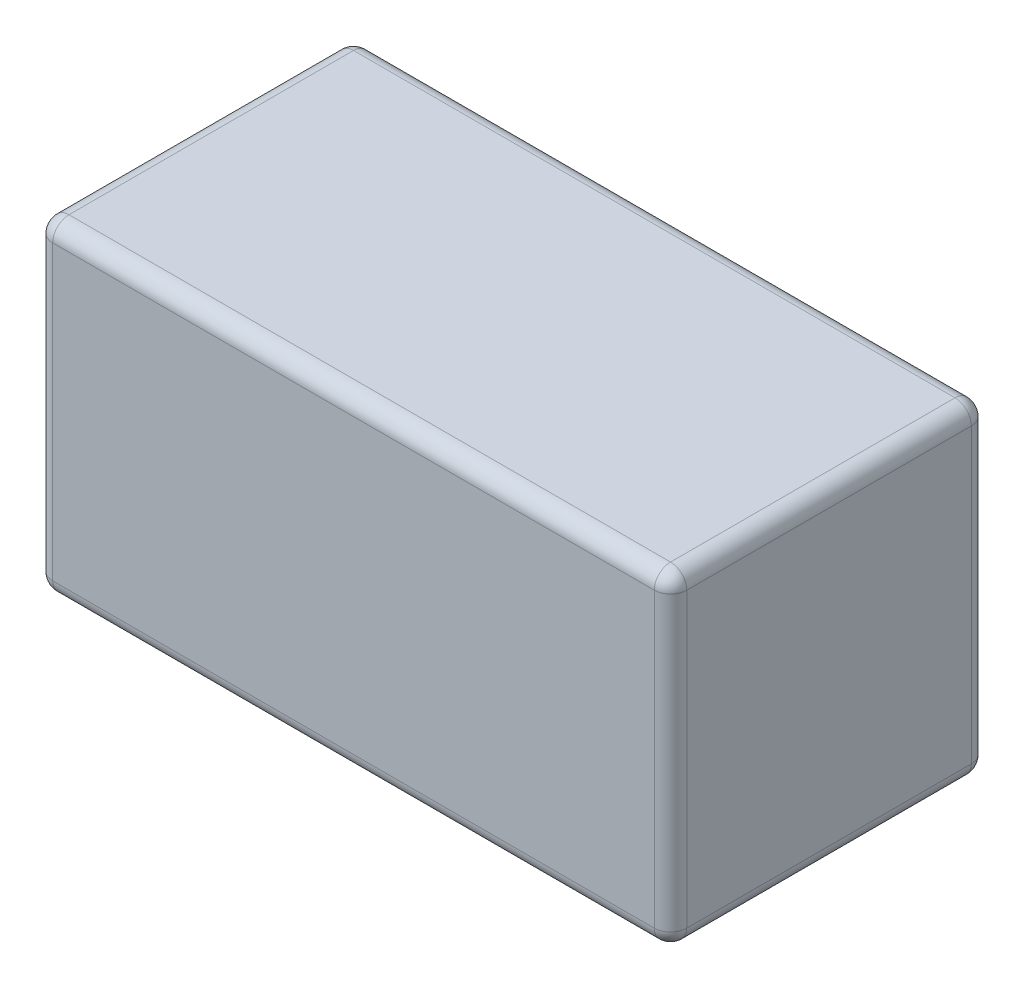
SolidWorks part; units mm, degrees
ref_plane "Front Plane" through (0, 0, 0) normal (0, 0, 1) x (1, 0, 0)
ref_plane "Top Plane" through (0, 0, 0) normal (0, 1, 0) x (1, 0, 0)
ref_plane "Right Plane" through (0, 0, 0) normal (1, 0, 0) x (0, 0, -1)
sketch "Sketch1" plane through (0, 0, 0) normal (0, 1, 0) x (1, 0, 0)
  line L1 (-39, 19.5) -> (39, 19.5)
  line L2 (-39, 19.5) -> (-39, -19.5)
  line L3 (-39, -19.5) -> (39, -19.5)
  line L4 (39, 19.5) -> (39, -19.5)
  line L5 (-39, 19.5) -> (39, -19.5) construction
  line L6 (-39, -19.5) -> (39, 19.5) construction
  point P0 (0, 0)
  dimension "D1" = 39
  dimension "D2" = 78
extrude "Boss-Extrude1" add sketch "Sketch1" along normal blind 40
fillet "Fillet1" radius 2 12 edges at (39, 20, 19.5) (0, 0, 19.5) (39, 0, 0) (-39, 20, 19.5) (-39, 0, 0) (0, 40, 19.5) (-39, 40, 0) (39, 40, 0) (39, 20, -19.5) (0, 40, -19.5) (-39, 20, -19.5) (0, 0, -19.5)
